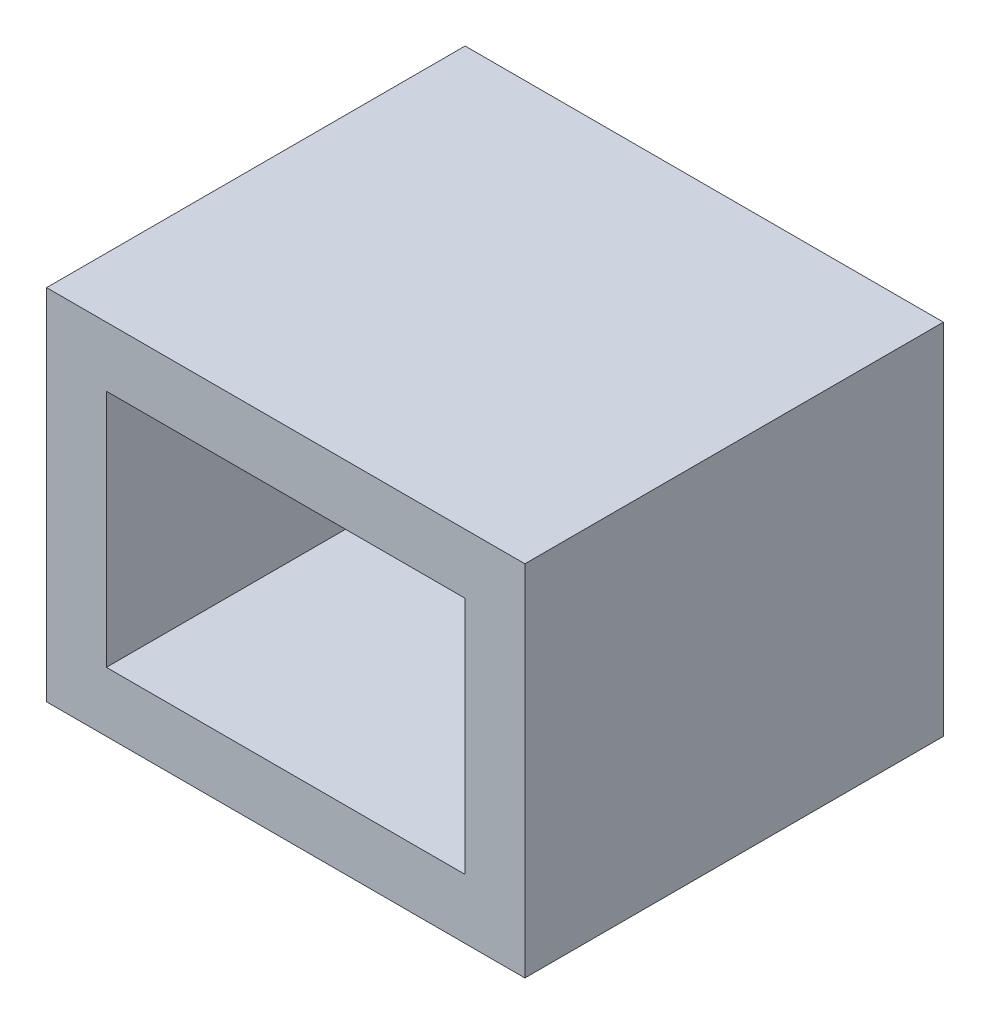
SolidWorks part; units mm, degrees
ref_plane "Alzado" through (0, 0, 0) normal (0, 0, 1) x (1, 0, 0)
ref_plane "Planta" through (0, 0, 0) normal (0, 1, 0) x (1, 0, 0)
ref_plane "Vista lateral" through (0, 0, 0) normal (1, 0, 0) x (0, 0, -1)
sketch "Croquis1" plane through (0, 0, 0) normal (0, 0, 1) x (1, 0, 0)
  line L1 (-27.4353, 6.8883) -> (-21.4353, 6.8883)
  line L2 (-27.4353, 6.8883) -> (-27.4353, 2.8883)
  line L3 (-27.4353, 2.8883) -> (-21.4353, 2.8883)
  line L4 (-21.4353, 6.8883) -> (-21.4353, 2.8883)
  line L5 (-28.4353, 7.8883) -> (-20.4353, 7.8883)
  line L6 (-28.4353, 7.8883) -> (-28.4353, 1.8883)
  line L7 (-28.4353, 1.8883) -> (-20.4353, 1.8883)
  line L8 (-20.4353, 7.8883) -> (-20.4353, 1.8883)
  dimension "D1" = 6
  dimension "D2" = 4
  dimension "D3" = 1
  dimension "D4" = 1
  dimension "D5" = 1
  dimension "D6" = 1
extrude "Saliente-Extruir1" add sketch "Croquis1" along normal blind 6
ref_plane "Plano1" through (-28.4353, 7.8883, 0) normal (-1, 0, 0) x (0, 0, 1)
sketch "Croquis3" plane through (0, 0, 0) normal (0, 0, -1) x (-1, 0, 0)
  line L1 (20.4353, 7.8883) -> (28.4353, 7.8883)
  line L2 (20.4353, 7.8883) -> (20.4353, 1.8883)
  line L3 (20.4353, 1.8883) -> (28.4353, 1.8883)
  line L4 (28.4353, 7.8883) -> (28.4353, 1.8883)
extrude "Saliente-Extruir2" add sketch "Croquis3" along normal blind 1
